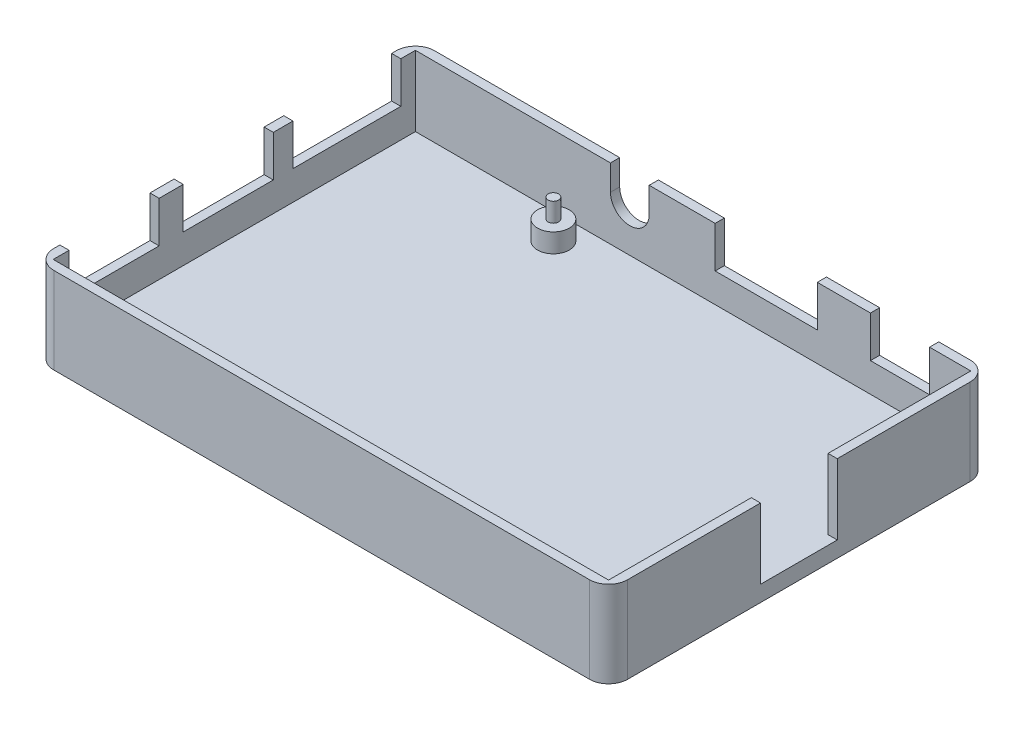
SolidWorks part; units mm, degrees
ref_plane "Alzado" through (0, 0, 0) normal (0, 0, 1) x (1, 0, 0)
ref_plane "Planta" through (0, 0, 0) normal (0, 1, 0) x (1, 0, 0)
ref_plane "Vista lateral" through (0, 0, 0) normal (1, 0, 0) x (0, 0, -1)
sketch "Croquis1" plane through (0, 0, 0) normal (0, 1, 0) x (1, 0, 0)
  line L1 (-42.5, -28) -> (42.5, -28) construction
  line L2 (-42.5, -28) -> (-42.5, 28) construction
  line L3 (-42.5, 28) -> (42.5, 28) construction
  line L4 (42.5, -28) -> (42.5, 28) construction
  line L5 (-42.5, -28) -> (42.5, 28) construction
  line L6 (-42.5, 28) -> (42.5, -28) construction
  line L7 (-44.5, -30) -> (44.5, -30)
  line L8 (-44.5, -30) -> (-44.5, 30)
  line L9 (-44.5, 30) -> (44.5, 30)
  line L10 (44.5, -30) -> (44.5, 30)
  line L11 (-44.5, -30) -> (44.5, 30) construction
  line L12 (-44.5, 30) -> (44.5, -30) construction
  point P0 (0, 0)
  point P6 (0, 0)
  dimension "D1" = 56
  dimension "D2" = 85
  dimension "D3" = 2
  dimension "D4" = 2
extrude "Saliente-Extruir1" add sketch "Croquis1" against normal blind 2.5
sketch "Croquis2" plane through (0, 0, 0) normal (0, 1, 0) x (1, 0, 0)
  line L1 (-42.5, -28) -> (42.5, -28) construction
  line L2 (-42.5, -28) -> (-42.5, 28) construction
  line L3 (-42.5, 28) -> (42.5, 28) construction
  line L4 (42.5, -28) -> (42.5, 28) construction
  line L5 (-42.5, -28) -> (42.5, 28) construction
  line L6 (-42.5, 28) -> (42.5, -28) construction
  line L7 (-44.5, 30) -> (-44.5, -30) construction
  circle A0 centre (40.75, 24.5) radius 2.5
  circle A1 centre (40.75, -24.5) radius 2.5
  circle A2 centre (-17.25, 24.5) radius 2.5
  circle A3 centre (-17.25, -24.5) radius 2.5
  point P0 (0, 0)
  dimension "D3" = 5
  dimension "D4" = 3.5
  dimension "D5" = 3.5
  dimension "D6" = 3.5
  dimension "D7" = 27.25
  dimension "D1" = 56
  dimension "D2" = 85
extrude "Saliente-Extruir2" add sketch "Croquis2" along normal blind 3
sketch "Croquis3" plane through (0, 3, 0) normal (0, 1, 0) x (1, 0, 0)
  circle A0 centre (-17.25, 24.5) radius 0.83
  circle A1 centre (40.75, 24.5) radius 0.83
  circle A2 centre (40.75, -24.5) radius 0.83
  circle A3 centre (-17.25, -24.5) radius 0.83
  dimension "D1" = 1.66
extrude "Saliente-Extruir3" add sketch "Croquis3" along normal blind 3
sketch "Croquis4" plane through (0, 0, 0) normal (0, 1, 0) x (1, 0, 0)
  line L0 (44.5, -30) -> (44.5, 30) construction
  line L1 (-42.5, -28) -> (42.5, -28) construction
  line L2 (-42.5, -28) -> (-42.5, 28) construction
  line L3 (-42.5, 28) -> (42.5, 28) construction
  line L4 (42.5, -28) -> (42.5, 28) construction
  line L5 (-42.5, -28) -> (42.5, 28) construction
  line L6 (-42.5, 28) -> (42.5, -28) construction
  line L7 (-44.5, -30) -> (44.5, -30)
  line L8 (-44.5, -30) -> (-44.5, -28.55)
  line L9 (-44.5, -28.55) -> (44.5, -28.55)
  line L10 (44.5, -30) -> (44.5, -28.55)
  line L12 (-44.5, 30) -> (44.5, 30)
  line L13 (-44.5, 30) -> (-44.5, 28.55)
  line L14 (-44.5, 28.55) -> (44.5, 28.55)
  line L15 (44.5, 30) -> (44.5, 28.55)
  point P0 (0, 0)
  dimension "D1" = 56
  dimension "D2" = 85
  dimension "D3" = 1.1
  dimension "D4" = 1.1
extrude "Saliente-Extruir4" add sketch "Croquis4" along normal blind 11.1
sketch "Croquis5" plane through (0, -2.5, 0) normal (0, -1, 0) x (1, 0, 0)
  line L0 (44.5, -30) -> (-44.5, -30) construction
  line L1 (44.5, 30) -> (45.95, 30)
  line L2 (44.5, 30) -> (44.5, -30)
  line L3 (44.5, -30) -> (45.95, -30)
  line L4 (45.95, 30) -> (45.95, -30)
  dimension "D1" = 1.45
extrude "Saliente-Extruir5" add sketch "Croquis5" against normal up to surface (13.6 mm away) up to face at (0, 11.1, 29.275)
sketch "Croquis6" plane through (0, 0, -30) normal (0, 0, -1) x (-1, 0, 0)
  line L0 (44.5, -2.5) -> (44.5, 11.1) construction
  line L1 (-45.95, 11.1) -> (44.5, 11.1) construction
  line L2 (6.2, 7.1) -> (6.2, 11.1)
  line L3 (6.2, 11.1) -> (12.3, 11.1)
  line L4 (12.3, 11.1) -> (12.3, 7.1)
  arc A0 (6.2, 7.1) -> (12.3, 7.1) centre (9.25, 7.1) ccw
  dimension "D2" = 6.1
  dimension "D3" = 4
  dimension "D1" = 35.25
extrude "Cortar-Extruir1" cut sketch "Croquis6" against normal up to next
sketch "Croquis7" plane through (0, 0, -30) normal (0, 0, -1) x (-1, 0, 0)
  line L0 (-45.95, -2.5) -> (44.5, -2.5) construction
  line L1 (-20.3, 11.1) -> (-4.2, 11.1)
  line L2 (-20.3, 11.1) -> (-20.3, 4.6)
  line L3 (-20.3, 4.6) -> (-4.2, 4.6)
  line L4 (-4.2, 11.1) -> (-4.2, 4.6)
  line L6 (-12.25, 11.1) -> (-12.25, 4.6) construction
  line L7 (44.5, -2.5) -> (44.5, 11.1) construction
  line L8 (-45.95, 11.1) -> (6.2, 11.1) construction
  dimension "D1" = 16.1
  dimension "D3" = 7.1
  dimension "D4" = 56.75
extrude "Cortar-Extruir2" cut sketch "Croquis7" against normal up to next
sketch "Croquis8" plane through (0, 0, -30) normal (0, 0, -1) x (-1, 0, 0)
  line L1 (-38, 11.1) -> (-28.68, 11.1)
  line L2 (-38, 11.1) -> (-38, 4.6)
  line L3 (-38, 4.6) -> (-28.68, 4.6)
  line L4 (-28.68, 11.1) -> (-28.68, 4.6)
  line L6 (-33.34, 11.1) -> (-33.34, 4.6) construction
  line L7 (-45.95, 11.1) -> (-45.95, -2.5) construction
  line L8 (-45.95, -2.5) -> (44.5, -2.5) construction
  line L9 (-45.95, 11.1) -> (-20.3, 11.1) construction
  dimension "D1" = 9.32
  dimension "D3" = 7.1
  dimension "D4" = 12.61
extrude "Cortar-Extruir3" cut sketch "Croquis8" against normal up to next
fillet "Redondeo1" radius 3 2 edges at (45.95, 4.3, 30) (45.95, 4.3, -30)
sketch "Croquis12" plane through (0, 0, 0) normal (0, 1, 0) x (1, 0, 0)
  line L0 (44.5, -28.55) -> (-44.5, -28.55) construction
  line L1 (-44.5, 28.55) -> (-43.05, 28.55)
  line L2 (-44.5, 28.55) -> (-44.5, -28.55)
  line L3 (-44.5, -28.55) -> (-43.05, -28.55)
  line L4 (-43.05, 28.55) -> (-43.05, -28.55)
  dimension "D1" = 1.45
extrude "Saliente-Extruir7" add sketch "Croquis12" along normal up to surface (11.1 mm away) up to face at (25.5043, 11.1, 0)
sketch "Croquis13" plane through (-44.5, 0, 0) normal (-1, 0, 0) x (0, 0, 1)
  line L0 (-30, 11.1) -> (30, 11.1) construction
  line L1 (-26.25, 4.6) -> (-9.25, 4.6)
  line L2 (-26.25, 4.6) -> (-26.25, 11.1)
  line L3 (-26.25, 11.1) -> (-9.25, 11.1)
  line L4 (-9.25, 4.6) -> (-9.25, 11.1)
  line L6 (-30, -2.5) -> (30, -2.5) construction
  line L7 (-17.75, 4.6) -> (-17.75, 11.1) construction
  line L8 (-30, -2.5) -> (-30, 11.1) construction
  dimension "D1" = 17
  dimension "D2" = 12.25
  dimension "D3" = 7.1
extrude "Cortar-Extruir5" cut sketch "Croquis13" against normal up to next
sketch "Croquis14" plane through (-44.5, 0, 0) normal (-1, 0, 0) x (0, 0, 1)
  line L0 (-9.25, 11.1) -> (30, 11.1) construction
  line L1 (-6.15, 11.1) -> (8.05, 11.1)
  line L2 (-6.15, 11.1) -> (-6.15, 4.6)
  line L3 (-6.15, 4.6) -> (8.05, 4.6)
  line L4 (8.05, 11.1) -> (8.05, 4.6)
  line L5 (-26.25, 4.6) -> (-9.25, 4.6) construction
  line L7 (0.95, 11.1) -> (0.95, 4.6) construction
  line L8 (11.85, 11.1) -> (26.05, 11.1)
  line L9 (11.85, 11.1) -> (11.85, 4.6)
  line L10 (11.85, 4.6) -> (26.05, 4.6)
  line L11 (26.05, 11.1) -> (26.05, 4.6)
  line L12 (18.95, 11.1) -> (18.95, 4.6) construction
  line L13 (-30, -2.5) -> (-30, 11.1) construction
  dimension "D1" = 14.2
  dimension "D2" = 30.95
  dimension "D3" = 14.2
  dimension "D4" = 48.95
extrude "Cortar-Extruir6" cut sketch "Croquis14" against normal up to next
fillet "Redondeo2" radius 3 2 edges at (-44.5, 4.3, 30) (-44.5, 4.3, -30)
sketch "Croquis15" plane through (0, 11.1, 0) normal (0, 1, 0) x (1, 0, 0)
  line L0 (0, 0) -> (45.95, 0) construction
  line L1 (45.95, -27) -> (45.95, 27) construction
  line L2 (44.5, 28.55) -> (44.5, -28.55) construction
  line L3 (44.5, -6.05) -> (45.95, -6.05)
  line L4 (44.5, -6.05) -> (44.5, 6.05)
  line L5 (44.5, 6.05) -> (45.95, 6.05)
  line L6 (45.95, -6.05) -> (45.95, 6.05)
  line L7 (44.5, 0) -> (45.95, 0) construction
  dimension "D1" = 12.1
extrude "Cortar-Extruir7" cut sketch "Croquis15" against normal up to surface (11.1 mm away) up to face at (40.75, 0, -27)
